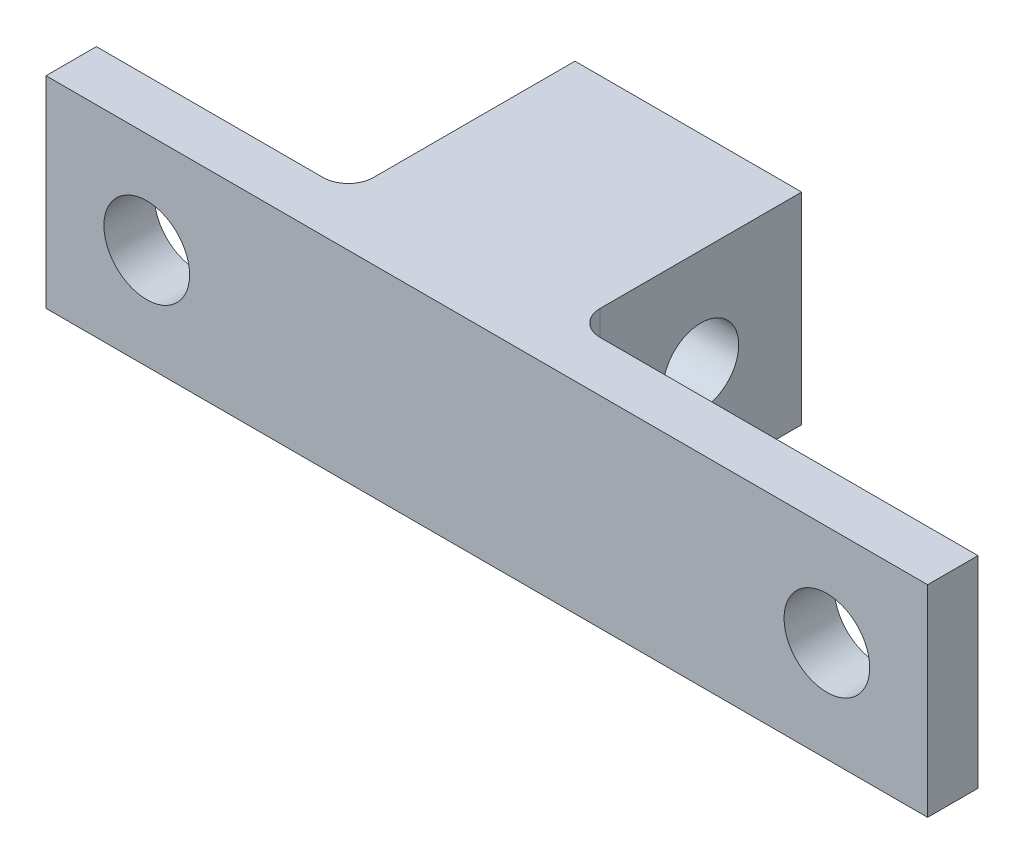
SolidWorks part; units mm, degrees
material "6061 Alloy"
ref_plane "Front Plane" through (0, 0, 0) normal (0, 0, 1) x (1, 0, 0)
ref_plane "Top Plane" through (0, 0, 0) normal (0, 1, 0) x (1, 0, 0)
ref_plane "Right Plane" through (0, 0, 0) normal (1, 0, 0) x (0, 0, -1)
sketch "Sketch1" plane through (0, 0, 0) normal (0, 1, 0) x (1, 0, 0)
  line L0 (0, 0) -> (10, 0)
  line L1 (10, 0) -> (10, 9)
  line L2 (10, 9) -> (19, 9)
  line L3 (19, 9) -> (19, 0)
  line L4 (19, 0) -> (35, 0)
  line L5 (35, 0) -> (35, -2)
  line L6 (35, -2) -> (0, -2)
  line L7 (0, -2) -> (0, 0)
  dimension "D1" = 2
  dimension "D2" = 11
  dimension "D3" = 10
  dimension "D4" = 16
  dimension "D5" = 9
extrude "Boss-Extrude1" add sketch "Sketch1" along normal blind 8 contours L1 L2 L3 L4 L5 L6 L7 L0
hole_wizard "M3 Clearance Hole1" positions "Sketch2" profile "Sketch3" hole size "M3" standard "ANSI Metric"
sketch "Sketch2" plane through (0, 0, 0) normal (0, 0, -1) x (-1, 0, 0)
  line L0 (-19, 8) -> (-35, 8) construction
  line L1 (-19, 8) -> (-19, 0) construction
  line L2 (0, 8) -> (-10, 8) construction
  line L3 (-10, 8) -> (-10, 0) construction
  point P0 (-4, 4)
  point P2 (-31, 4)
  dimension "D1" = 4
  dimension "D2" = 12
  dimension "D3" = 4
  dimension "D4" = 6
sketch "Sketch3" plane through (4, 4, 0) normal (1, 0, 0) x (0, 1, 0)
  line L0 (0, 0) -> (0, 4.9215)
  line L1 (0, 4.9215) -> (1.7, 3.9)
  line L2 (1.7, 3.9) -> (1.7, 0)
  line L5 (1.7, 0) -> (0, 0)
  line L10 (0, 4.9215) -> (-1.7, 3.9) construction
  line L11 (0, -6.35) -> (0, 107.95) construction
  dimension "Hole Dia." = 3.4
  dimension "Hole Depth" = 3.9
  dimension "Drill Angle" = 118
sketch "Sketch4" plane through (10, 0, 0) normal (-1, 0, 0) x (0, 0, 1)
  line L0 (0, 8) -> (0, 0) construction
  line L1 (0, 0) -> (-9, 0) construction
  circle A0 centre (-5, 4) radius 1.5
  dimension "D1" = 3
  dimension "D2" = 5
  dimension "D3" = 4
extrude "Cut-Extrude1" cut sketch "Sketch4" against normal through all
fillet "Fillet1" radius 1 2 edges at (10, 4, 0) (19, 4, 0)
